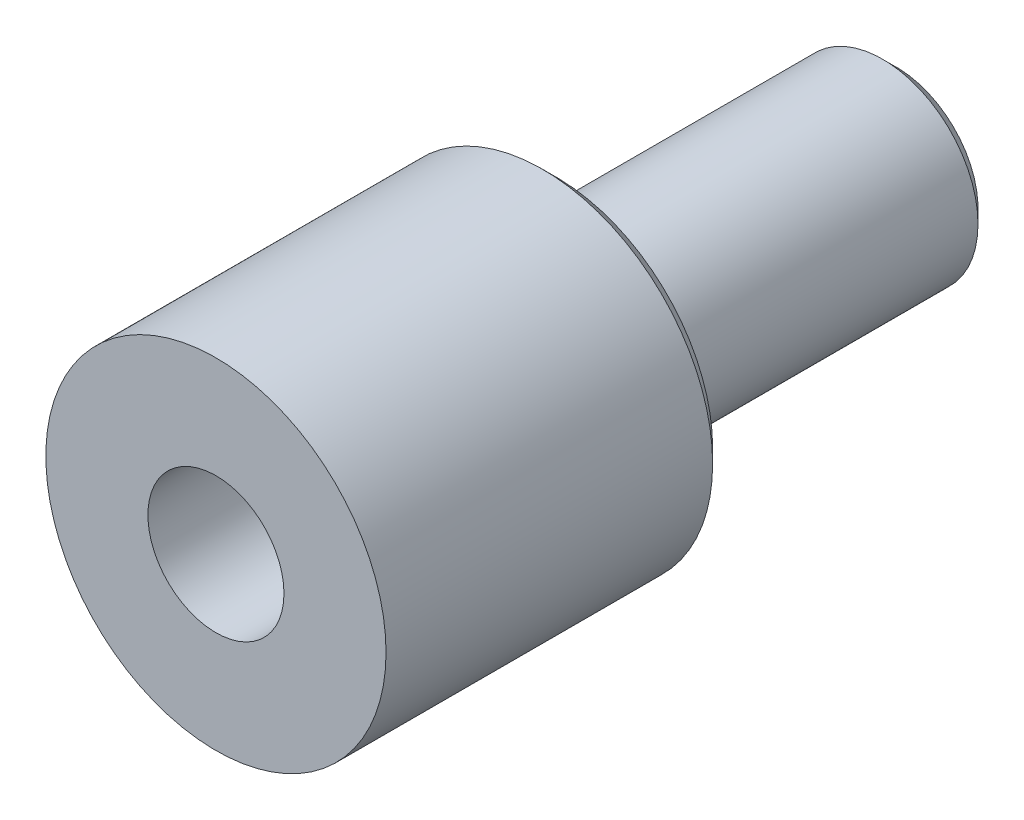
SolidWorks part; units mm, degrees
material "AISI 1020 Steel, Cold Rolled"
ref_plane "Front Plane" through (0, 0, 0) normal (0, 0, 1) x (1, 0, 0)
ref_plane "Top Plane" through (0, 0, 0) normal (0, 1, 0) x (1, 0, 0)
ref_plane "Right Plane" through (0, 0, 0) normal (1, 0, 0) x (0, 0, -1)
sketch "Sketch1" plane through (0, 0, 0) normal (0, 0, 1) x (1, 0, 0)
  circle A0 centre (0, 0) radius 12.5
  circle A1 centre (0, 0) radius 5
  dimension "D1" = 25
  dimension "D2" = 10
extrude "Boss-Extrude1" add sketch "Sketch1" along normal blind 25
sketch "Sketch3" plane through (0, 0, 0) normal (0, 0, -1) x (-1, 0, 0)
  circle A1 centre (0, 0) radius 7
  dimension "D2" = 14
extrude "Boss-Extrude2" add sketch "Sketch3" along normal blind 25
chamfer "Chamfer1" distance 1 angle 45 1 edges at (12.5, 0, 0)
chamfer "Chamfer2" distance 1 angle 45 1 edges at (-7, 0, -25)
sketch "Sketch5" plane through (0, 0, 0) normal (1, 0, 0) x (0, 0, -1)
  line L0 (-63.8307, 0) -> (70.3846, 0) construction
